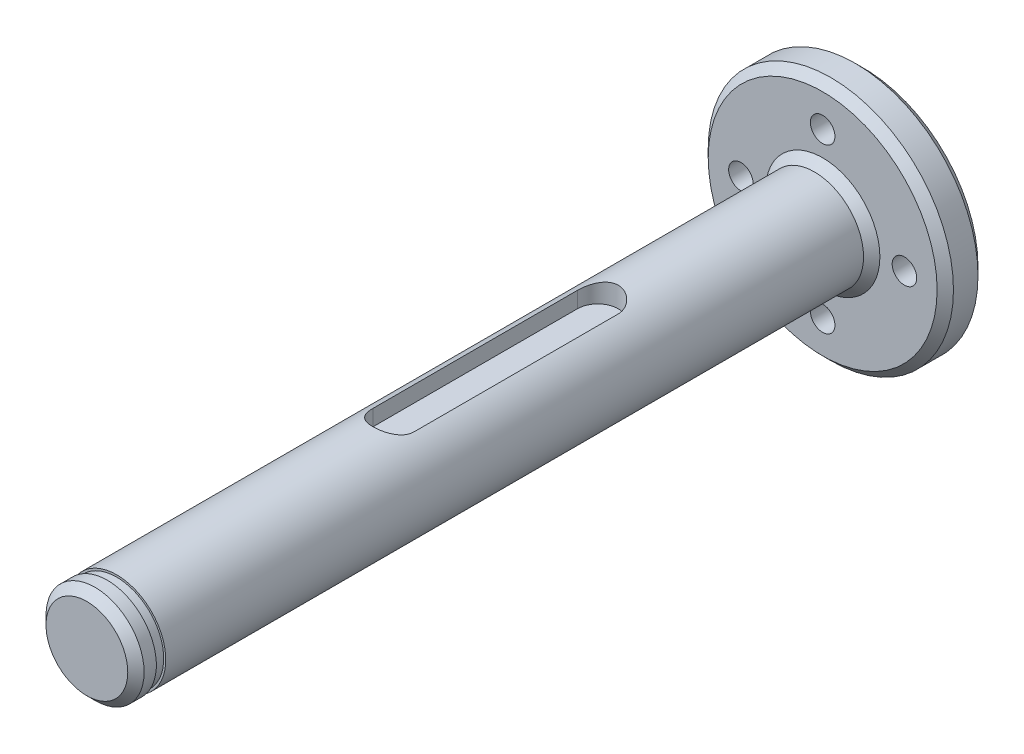
SolidWorks part; units mm, degrees
material "Chrome Stainless Steel"
ref_plane "Front Plane" through (0, 0, 0) normal (0, 0, 1) x (1, 0, 0)
ref_plane "Top Plane" through (0, 0, 0) normal (0, 1, 0) x (1, 0, 0)
ref_plane "Right Plane" through (0, 0, 0) normal (1, 0, 0) x (0, 0, -1)
sketch "Sketch1" plane through (0, 0, 0) normal (0, 0, 1) x (1, 0, 0)
  circle A0 centre (0, 0) radius 15
  arc A2 (-13.5728, 6.3859) -> (14.6642, 3.1563) centre (0, 0) ccw construction
  arc A3 (14.6642, 3.1563) -> (-13.5728, 6.3859) centre (0, 0) ccw construction
  dimension "D1" = 30
extrude "Boss-Extrude1" add sketch "Sketch1" along normal blind 5
sketch "Sketch4" plane through (0, 0, 0) normal (0, 0, -1) x (-1, 0, 0)
  line L0 (0, 10) -> (0, -10) construction
  line L1 (0, -10) -> (-10, 0) construction
  line L2 (-10, 0) -> (10, 0) construction
  circle A0 centre (10, 0) radius 1.5
  circle A1 centre (0, -10) radius 1.5
  circle A2 centre (-10, 0) radius 1.5
  circle A3 centre (0, 10) radius 1.5
  dimension "D1" = 3
extrude "Cut-Extrude2" cut sketch "Sketch4" against normal through all both
sketch "Sketch6" plane through (0, 0, 5) normal (0, 0, 1) x (1, 0, 0)
  circle A0 centre (0, 0) radius 6
  dimension "D1" = 12
extrude "Boss-Extrude2" add sketch "Sketch6" along normal blind 90
chamfer "Chamfer1" distance 1 angle 45 4 edges at (6, 0, 95) (6, 0, 5) (15, 0, 5) (15, 0, 0)
ref_plane "Plane1" through (0, 6, 0) normal (0, 1, 0) x (1, 0, 0)
sketch "Sketch7" plane through (0, 6, 0) normal (0, 1, 0) x (1, 0, 0)
  line L0 (0, -95) -> (0, 0) construction
  line L1 (-5, -95) -> (5, -95) construction
  line L2 (0, -57.5) -> (0, -32.5) construction
  line L3 (-2.5, -57.5) -> (-2.5, -32.5)
  line L4 (2.5, -57.5) -> (2.5, -32.5)
  arc A0 (-2.5, -57.5) -> (2.5, -57.5) centre (0, -57.5) ccw
  arc A1 (2.5, -32.5) -> (-2.5, -32.5) centre (0, -32.5) ccw
  point P7 (0, -45)
  point P12 (0, -30)
  point P13 (0, -60)
  dimension "D1" = 5
  dimension "D2" = 30
  dimension "D3" = 30
extrude "Cut-Extrude3" cut sketch "Sketch7" against normal blind 2.5
sketch "Sketch8" plane through (0, 0, 0) normal (0, 1, 0) x (1, 0, 0)
  line L0 (0, 0) -> (0, -95) construction
  line L1 (-5, -95) -> (5, -95) construction
  line L2 (-6, -6) -> (-6, -94) construction
  line L3 (-6, -92.5) -> (-5.75, -92.5)
  line L4 (-6, -92.5) -> (-6, -91.35)
  line L5 (-6, -91.35) -> (-5.75, -91.35)
  line L6 (-5.75, -92.5) -> (-5.75, -91.35)
  dimension "D1" = 11.5
  dimension "D2" = 1.15
  dimension "D3" = 2.5
revolve "Cut-Revolve1" cut sketch "Sketch8" angle 360 about L0
hole_wizard "Ø5.0mm Dowel Hole1" positions "Sketch9" profile "Sketch10" hole size "Ø5.0" standard "DIN"
sketch "Sketch9" plane through (0, 0, 0) normal (0, 0, -1) x (-1, 0, 0)
  point P0 (0, 0)
sketch "Sketch10" plane through (0, 0, 0) normal (1, 0, 0) x (0, 1, 0)
  line L0 (0, 0) -> (0, 9.0022)
  line L1 (0, 9.0022) -> (2.5, 7.5)
  line L2 (2.5, 7.5) -> (2.5, 0)
  line L5 (2.5, 0) -> (0, 0)
  line L10 (0, 9.0022) -> (-2.5, 7.5) construction
  line L11 (0, -6.35) -> (0, 107.95) construction
  dimension "Hole Dia." = 5
  dimension "Hole Depth" = 7.5
  dimension "Drill Angle" = 118
chamfer "Chamfer2" distance 1 angle 45 1 edges at (-2.5, 0, 0)
